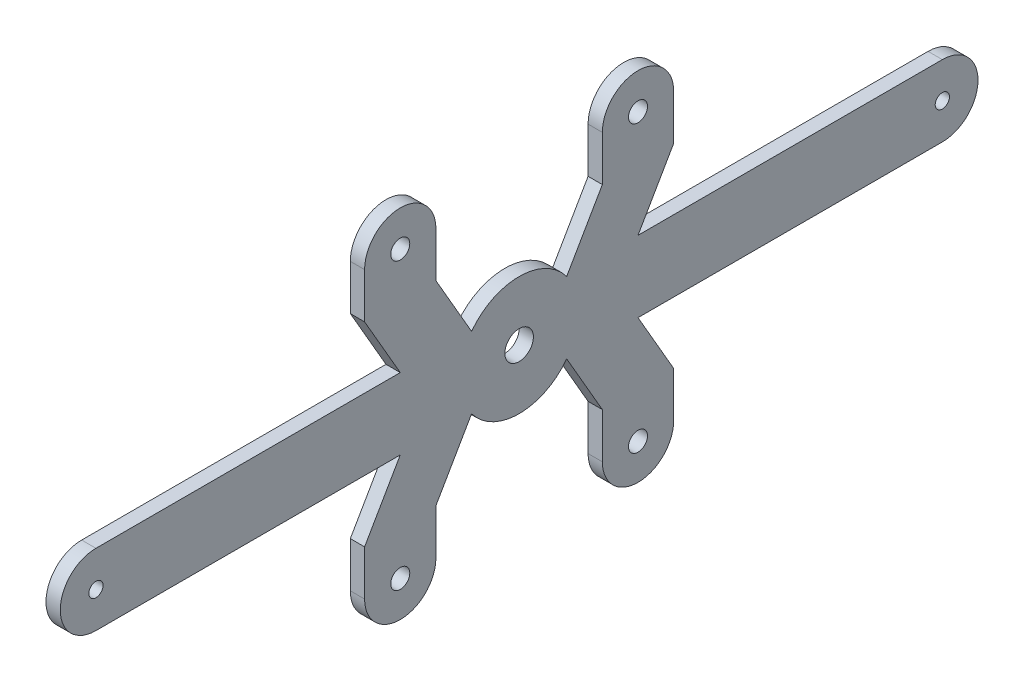
SolidWorks part; units mm, degrees
material "Acrylic (Medium-high impact)"
ref_plane "Front Plane" through (0, 0, 0) normal (0, 0, 1) x (1, 0, 0)
ref_plane "Top Plane" through (0, 0, 0) normal (0, 1, 0) x (1, 0, 0)
ref_plane "Right Plane" through (0, 0, 0) normal (1, 0, 0) x (0, 0, -1)
sketch "Sketch1" plane through (0, 0, 0) normal (1, 0, 0) x (0, 0, -1)
  line L0 (0, 0) -> (-114.2997, 0) construction
  line L1 (105, -45) -> (-105, -45)
  line L2 (105, -45) -> (105, 45)
  line L3 (105, 45) -> (-105, 45)
  line L4 (-105, -45) -> (-105, 45)
  line L5 (105, -45) -> (-105, 45) construction
  line L6 (105, 45) -> (-105, -45) construction
  point P0 (0, 0)
  dimension "D1" = 210
  dimension "D2" = 90
extrude "Boss-Extrude1" add sketch "Sketch1" along normal blind 3
sketch "Sketch2" plane through (3, 0, 0) normal (1, 0, 0) x (0, 0, -1)
  circle A2 centre (-89, 0) radius 1.5
  dimension "D1" = 3
  dimension "D2" = 89
extrude "Cut-Extrude1" cut sketch "Sketch2" against normal through all
sketch "Sketch3" plane through (3, 0, 0) normal (1, 0, 0) x (0, 0, -1)
  line L0 (0, 55) -> (0, -55) construction
  line L1 (55, 0) -> (-55, 0) construction
  circle A0 centre (-25, 30) radius 2
  dimension "D1" = 4
  dimension "D2" = 25
  dimension "D3" = 30
extrude "Cut-Extrude2" cut sketch "Sketch3" against normal through all
sketch "Sketch4" plane through (3, 0, 0) normal (1, 0, 0) x (0, 0, -1)
  line L2 (-105, 0) -> (-105, 45)
  line L12 (-32.5, 30) -> (-32.5, 20.4904)
  line L16 (-89, 7.5) -> (-25, 7.5)
  line L17 (-96.5, 0) -> (-105, 0)
  line L19 (0, 40) -> (0, 45)
  line L20 (105, 45) -> (-105, 45) construction
  line L21 (0, 45) -> (-105, 45)
  line L24 (0, 12.5) -> (0, 40)
  line L29 (-17.5, 30) -> (-17.5, 20.4904)
  line L30 (-32.5, 20.4904) -> (-25, 7.5)
  line L31 (-17.5, 20.4904) -> (-10, 7.5)
  circle A19 centre (-89, 0) radius 1.5 construction
  arc A30 (-89, 7.5) -> (-96.5, 0) centre (-89, 0) ccw
  arc A33 (-17.5, 30) -> (-32.5, 30) centre (-25, 30) ccw
  arc A41 (0, 12.5) -> (-10, 7.5) centre (0, 0) ccw
  dimension "D1" = 7.5
  dimension "D2" = 15
  dimension "D3" = 25
  dimension "D4" = 0
  dimension "D5" = 60
extrude "Cut-Extrude3" cut sketch "Sketch4" against normal through all
mirror "Mirror2" about plane through (0, 0, 0) normal (0, 1, 0) of "Cut-Extrude3", "Cut-Extrude2"
mirror "Mirror3" about plane through (0, 0, 0) normal (0, 0, 1) of "Mirror2", "Cut-Extrude3", "Cut-Extrude1", "Cut-Extrude2"
sketch "Sketch5" plane through (3, 0, 0) normal (1, 0, 0) x (0, 0, -1)
  circle A0 centre (0, 0) radius 3
  dimension "D1" = 6
extrude "Cut-Extrude4" cut sketch "Sketch5" against normal through all
